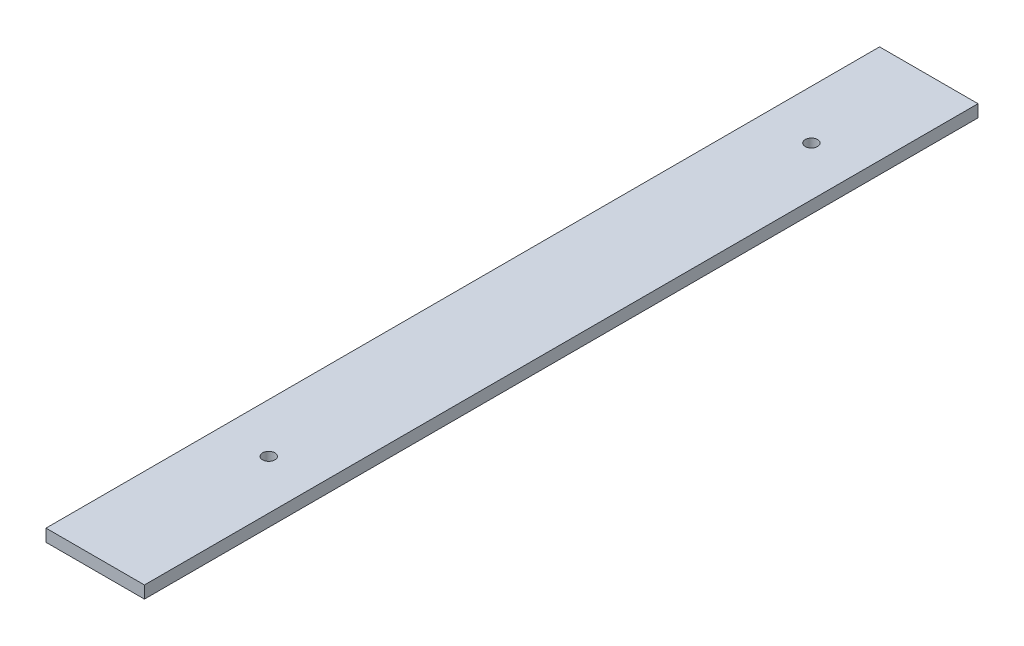
SolidWorks part; units mm, degrees
material "6063-O"
ref_plane "Front Plane" through (0, 0, 0) normal (0, 0, 1) x (1, 0, 0)
ref_plane "Top Plane" through (0, 0, 0) normal (0, 1, 0) x (1, 0, 0)
ref_plane "Right Plane" through (0, 0, 0) normal (1, 0, 0) x (0, 0, -1)
sketch "Sketch4" plane through (0, 0, 0) normal (0, 1, 0) x (1, 0, 0)
  line L4 (23232.9446, -10111.0305) -> (23232.9446, -10251.0305) construction
  line L5 (23232.9446, -9942.5829) -> (23032.9446, -9942.5829)
  line L6 (23232.9446, -9942.5829) -> (23232.9446, -12876.1567)
  line L7 (23232.9446, -12876.1567) -> (23032.9446, -12876.1567)
  line L8 (23032.9446, -9942.5829) -> (23032.9446, -12876.1567)
  line L9 (22132.9446, -9942.5829) -> (21932.9446, -9942.5829)
  line L10 (22132.9446, -9942.5829) -> (22132.9446, -12833.5838)
  line L11 (22132.9446, -12833.5838) -> (21932.9446, -12833.5838)
  line L12 (21932.9446, -9942.5829) -> (21932.9446, -12833.5838)
  line L13 (20932.9446, -9942.5829) -> (20732.9446, -9942.5829)
  line L14 (20932.9446, -9942.5829) -> (20932.9446, -12599.4325)
  line L15 (20932.9446, -12599.4325) -> (20732.9446, -12599.4325)
  line L16 (20732.9446, -9942.5829) -> (20732.9446, -12599.4325)
  line L17 (19732.9446, -9942.5829) -> (19532.9446, -9942.5829)
  line L18 (19732.9446, -9942.5829) -> (19732.9446, -12109.8436)
  line L19 (19732.9446, -12109.8436) -> (19532.9446, -12109.8436)
  line L20 (19532.9446, -9942.5829) -> (19532.9446, -12109.8436)
  line L21 (18902.9446, -9942.5829) -> (18702.9446, -9942.5829)
  line L22 (18902.9446, -9942.5829) -> (18902.9446, -11636.2195)
  line L23 (18902.9446, -11636.2195) -> (18702.9446, -11636.2195)
  line L24 (18702.9446, -9942.5829) -> (18702.9446, -11636.2195)
  line L25 (18702.9446, -10111.0305) -> (18702.9446, -10251.0305) construction
  line L26 (23132.9446, -12748.1199) -> (23132.9446, -12608.0593) construction
  line L27 (22032.9446, -12550.6075) -> (22032.9446, -12691.8491) construction
  line L28 (20832.9446, -12422.3488) -> (20832.9446, -12275.1597) construction
  line L29 (19632.9446, -11906.9658) -> (19632.9446, -11746.8651) construction
  line L30 (18802.9446, -11371.765) -> (18802.9446, -11195.5746) construction
  line L31 (23132.9446, -10251.0305) -> (23132.9446, -10111.0305) construction
  line L32 (18702.9446, -10251.0305) -> (23232.9446, -10251.0305) construction
  line L33 (23232.9446, -10111.0305) -> (18702.9446, -10111.0305) construction
  circle A0 centre (23132.9446, -12678.0896) radius 12.5
  arc A1 (18702.9446, -11295.1434) -> (23232.9446, -12744.4799) centre (22932.9446, -5878.0705) ccw construction
  arc A2 (18702.9446, -11116.3765) -> (23232.9446, -12604.3436) centre (22932.9446, -5878.0705) ccw construction
  circle A3 centre (22032.9446, -12621.2283) radius 12.5
  circle A4 centre (20832.9446, -12348.7542) radius 12.5
  circle A5 centre (19632.9446, -11826.9154) radius 12.5
  circle A6 centre (18802.9446, -11283.6698) radius 12.5
  circle A7 centre (18802.9446, -10181.0305) radius 12.5
  circle A8 centre (19632.9446, -10181.0305) radius 12.5
  circle A9 centre (20832.9446, -10181.0305) radius 12.5
  circle A10 centre (22032.9446, -10181.0305) radius 12.5
  circle A11 centre (23132.9446, -10181.0305) radius 12.5
  arc A12 (18702.9446, -11116.3765) -> (23232.9446, -12604.3436) centre (22932.9446, -5878.0705) ccw construction
  point P22 (23132.9446, -9942.5829)
  point P23 (22032.9446, -9942.5829)
  point P24 (20832.9446, -9942.5829)
  point P25 (19632.9446, -9942.5829)
  point P26 (23132.9446, -12876.1567)
  point P30 (20832.9446, -12599.4325)
  point P40 (23132.9446, -12678.0896)
  point P59 (22032.9446, -12621.2283)
  point P60 (22032.9446, -12833.5838)
  point P68 (20832.9446, -12348.7542)
  point P69 (19632.9446, -12109.8436)
  point P73 (19632.9446, -11826.9154)
  point P74 (18802.9446, -11283.6698)
  point P75 (18802.9446, -11636.2195)
  point P78 (23132.9446, -10181.0305)
  point P91 (18802.9446, -9942.5829)
  dimension "D5" = 25
  dimension "D1" = 200
  dimension "D2" = 1200
  dimension "D3" = 1200
  dimension "D4" = 1200
  dimension "D6" = 100
  dimension "D7" = 70
extrude "Boss-Extrude1" add sketch "Sketch4" along normal blind 25
sketch "Sketch5" plane through (0, 0, 0) normal (0, 1, 0) x (1, 0, 0)
  line L1 (25145.0991, -8844.9142) -> (19082.0563, -8844.9142)
  line L2 (25145.0991, -8844.9142) -> (25145.0991, -13797.5742)
  line L3 (25145.0991, -13797.5742) -> (19082.0563, -13797.5742)
  line L4 (19082.0563, -8844.9142) -> (19082.0563, -13797.5742)
extrude "Cut-Extrude1" cut sketch "Sketch5" along normal through all
